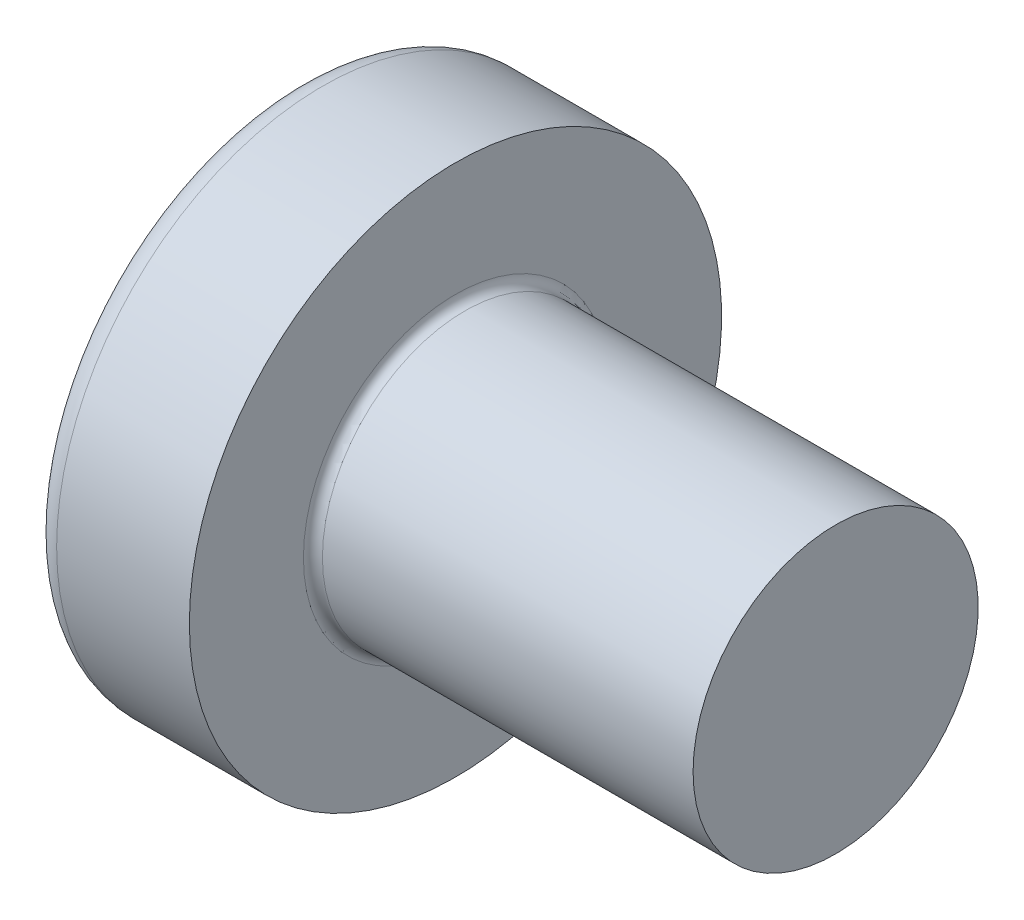
SolidWorks part; units mm, degrees
ref_plane "Plane1" through (0, 0, 0) normal (0, 0, 1) x (1, 0, 0)
ref_plane "Plane2" through (0, 0, 0) normal (0, 1, 0) x (1, 0, 0)
ref_plane "Plane3" through (0, 0, 0) normal (1, 0, 0) x (0, 0, -1)
sketch "BodySke" plane through (0, 0, 0) normal (0, 0, 1) x (1, 0, 0)
  line L0 (2.4, 1.5) -> (2.4, 2.8)
  line L1 (2.65, 6.35) -> (2.65, -3.175) construction
  line L2 (-25.4, 0) -> (127, 0) construction
  line L3 (6.4, 0) -> (0, 0)
  line L4 (2.4, 1.5) -> (6.4, 1.5)
  line L5 (6.4, 1.5) -> (6.4, 0)
  line L6 (1.0035, 2.8) -> (2.4, 2.8)
  line L8 (0.4, 6.35) -> (0.4, -3.175) construction
  arc A0 (0.7754, 2.6744) -> (0, 0) centre (5, 0) ccw
  arc A2 (0.7754, 2.6744) -> (1.0035, 2.8) centre (1.0035, 2.53) cw
  dimension "Head_fillet_rad" = 0.27
  dimension "Head_crown_rad" = 5
  dimension "Head_ht" = 2.4
  dimension "Diameter" = 3
  dimension "Length" = 4
  dimension "Head_dia" = 5.6
  dimension "Advance" = 0.5
  dimension "Thread_nom" = 6
revolve "Base-Revolve" add sketch "BodySke"
cosmetic thread "ThreadCosmetic" [suppressed]
fillet "Fillet1" radius 0.1 1 edges at (2.4, 0, 1.5)
sketch "Sketch3" plane through (0, 0, 0) normal (1, 0, 0) x (0, 0, -1)
  line L0 (0.37, -1.4) -> (-0.37, -1.4)
  line L1 (0.37, -1.4) -> (0.37, 1.4)
  line L2 (-0.37, 1.4) -> (0.37, 1.4)
  line L3 (-0.37, 1.4) -> (-0.37, -1.4)
  dimension "D1" = 1.4
  dimension "Cross_dia" = 2.8
  dimension "D2" = 0.37
  dimension "Cross_width" = 0.74
ref_plane "Plane4" through (1.75, 0, 0) normal (1, 0, 0) x (0, 0, -1)
sketch "Sketch4" plane through (1.75, 0, 0) normal (1, 0, 0) x (0, 0, -1)
  line L0 (0.37, -0.5275) -> (-0.37, -0.5275)
  line L1 (0.37, -0.5275) -> (0.37, 0.5275)
  line L2 (-0.37, 0.5275) -> (0.37, 0.5275)
  line L3 (-0.37, 0.5275) -> (-0.37, -0.5275)
  dimension "D1" = 0.74
  dimension "D2" = 1.055
  dimension "D3" = 0.37
  dimension "D4" = 0.5275
loft "Recess" cut profiles "Sketch3", "Sketch4"
pattern_circular "RecPat" count 2 every 90 about axis through (0, 0, 0) along (1, 0, 0) of "Recess"
sketch "RecCorSke" plane through (0, 0, 0) normal (0, 0, 1) x (1, 0, 0)
  line L0 (-3.175, 0) -> (15.875, 0) construction
  line L1 (-25.4, 0) -> (127, 0) construction
  line L2 (0, 0) -> (0, 0.6784)
  line L3 (0, 0.6784) -> (1.75, 0.556)
  line L4 (1.75, 0.556) -> (1.9307, 0)
  line L5 (1.9307, 0) -> (0, 0)
  dimension "Diameter" = 1.112
  dimension "Depth" = 1.75
  dimension "Draft_angle" = 4
  dimension "Bottom_angle" = 18
revolve "RecessCore" cut sketch "RecCorSke" angle 360 about L0
sketch "ThdSchSke" plane through (0, 0, 0) normal (0, 0, 1) x (1, 0, 0)
  line L0 (3.4, -1.2195) -> (3.2036, -1.5)
  line L1 (3.4, -1.2195) -> (3.5964, -1.5)
  line L2 (3.5964, -1.5) -> (3.5964, -1.875)
  line L3 (-3.175, 0) -> (5.1513, 0) construction
  line L5 (3.5964, -1.875) -> (3.2036, -1.875)
  line L6 (3.2036, -1.875) -> (3.2036, -1.5)
  dimension "Thread_minor" = 2.439
  dimension "Diameter" = 3
  dimension "Start" = 3.4
  dimension "SideAngle" = 55
  dimension "VeeAngle" = 70
  dimension "Overcut" = 3.75
revolve "ThreadSchematic" [suppressed] cut sketch "ThdSchSke" angle 360 about L3
pattern_linear "ThdSchPat" [suppressed]
equation "\"D1@Sketch3\" = \"Cross_dia@Sketch3\" / 2"
equation "\"D2@Sketch3\" = \"Cross_width@Sketch3\" / 2"
equation "\"Depth@RecCorSke\" = \"Cross_depth@Plane4\""
equation "\"D1@Sketch4\" = \"Cross_width@Sketch3\""
equation "\"D2@Sketch4\" = \"Cross_dia@Sketch3\" - 2.0 * \"Cross_depth@Plane4\" * tan(26.5  * 0.017453292)"
equation "\"D3@Sketch4\" = \"D1@Sketch4\" / 2"
equation "\"D4@Sketch4\" = \"D2@Sketch4\" / 2"
equation "\"Thread_length@ThreadCosmetic\" = ((sgn( (\"Length@BodySke\" - \"Advance@BodySke\" * 2.0 ) - \"Thread_nom@BodySke\" )-1)*( (\"Length@BodySke\" - \"Advance@BodySke\" * 2.0 ) - \"Thread_nom@BodySke\" ))/-2+ \"Thread_nom@BodySke\""
equation "\"Thread_minor@ThdSchSke\" = \"Thread_minor@ThreadCosmetic\""
equation "\"Diameter@ThdSchSke\" = \"Diameter@BodySke\""
equation "\"Overcut@ThdSchSke\" = \"Diameter@BodySke\" * 1.25"
equation "\"Start@ThdSchSke\" = \"Head_ht@BodySke\" + \"Length@BodySke\" - \"Thread_length@ThreadCosmetic\"  '---Non-countersunk---"
equation "\"Num_threads@ThdSchPat\" = int( \"Thread_length@ThreadCosmetic\" / \"Advance@BodySke\" + 0.999 )  + 1"
equation "\"Advance@ThdSchPat\" = \"Thread_length@ThreadCosmetic\" /  (\"Num_threads@ThdSchPat\" - 1) 'relax it"
